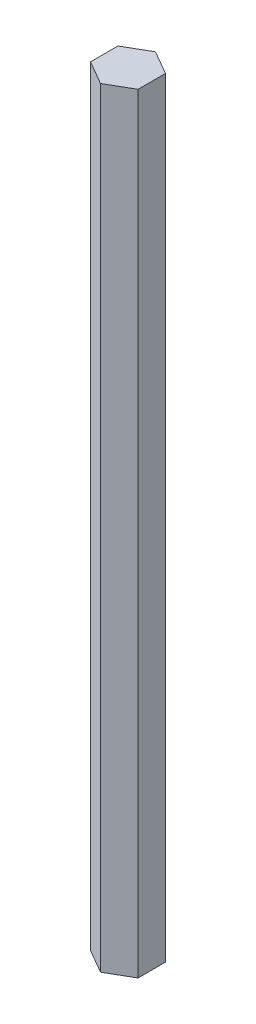
SolidWorks part; units mm, degrees
ref_plane "Front Plane" through (0, 0, 0) normal (0, 0, 1) x (1, 0, 0)
ref_plane "Top Plane" through (0, 0, 0) normal (0, 1, 0) x (1, 0, 0)
ref_plane "Right Plane" through (0, 0, 0) normal (1, 0, 0) x (0, 0, -1)
sketch "Sketch1" plane through (0, 0, 0) normal (0, 1, 0) x (1, 0, 0)
  line L8 (-5.2793, -3.048) -> (0, -6.096)
  line L9 (0, -6.096) -> (5.2793, -3.048)
  line L10 (5.2793, -3.048) -> (5.2793, 3.048)
  line L11 (5.2793, 3.048) -> (0, 6.096)
  line L12 (0, 6.096) -> (-5.2793, 3.048)
  line L13 (-5.2793, 3.048) -> (-5.2793, -3.048)
  circle A2 centre (0, 0) radius 6.096 construction
  dimension "D1" = 12.192
extrude "Boss-Extrude1" add sketch "Sketch1" along normal blind 170.9242
